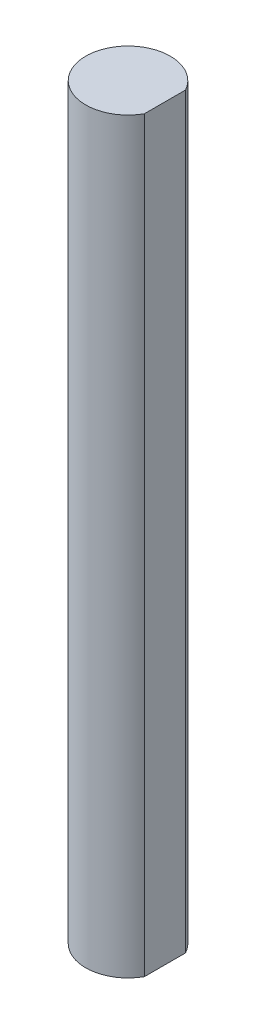
SolidWorks part; units mm, degrees
ref_plane "Front Plane" through (0, 0, 0) normal (0, 0, 1) x (1, 0, 0)
ref_plane "Top Plane" through (0, 0, 0) normal (0, 1, 0) x (1, 0, 0)
ref_plane "Right Plane" through (0, 0, 0) normal (1, 0, 0) x (0, 0, -1)
sketch "Sketch1" plane through (0, 0, 0) normal (0, 1, 0) x (1, 0, 0)
  line L0 (2.5116, 1.399) -> (2.5116, -1.399)
  arc A0 (2.5116, 1.399) -> (2.5116, -1.399) centre (0, 0) ccw
  dimension "D1" = 5.75
  dimension "D2" = 2.7981
extrude "Boss-Extrude1" add sketch "Sketch1" along normal blind 50.8
